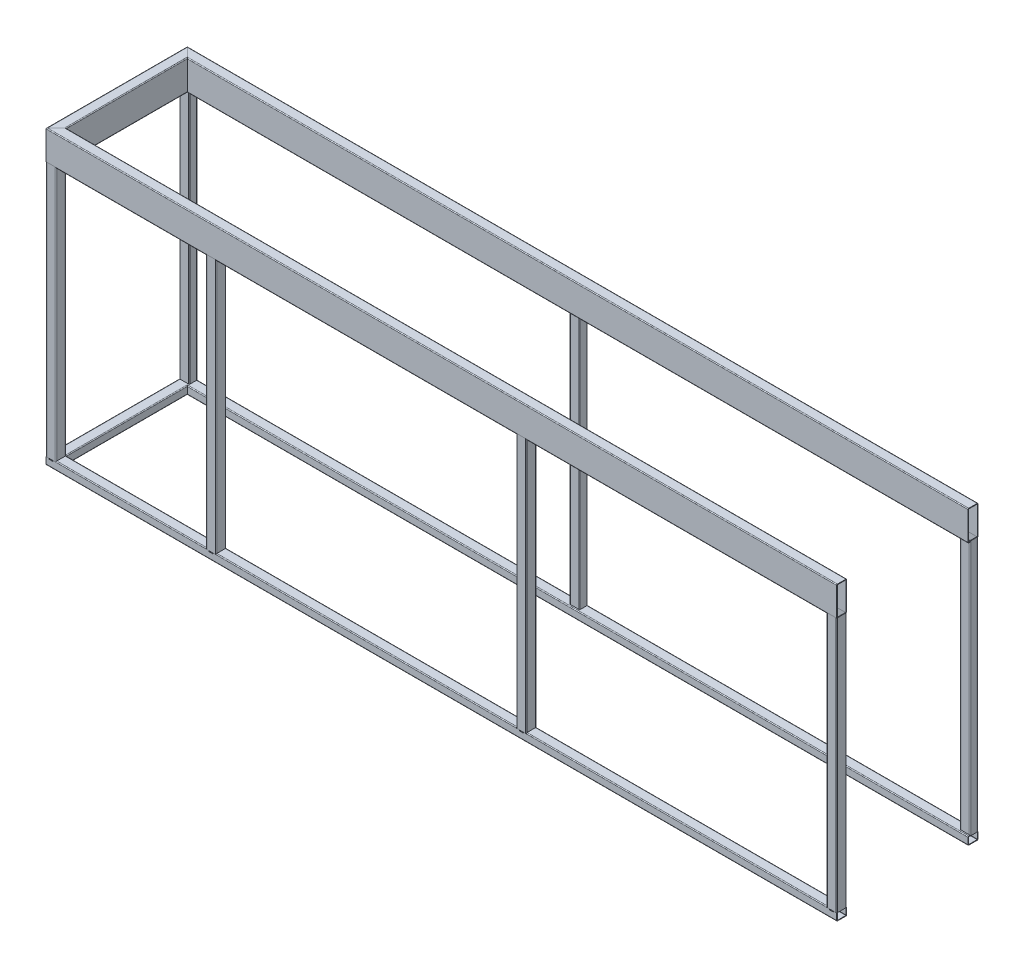
SolidWorks part; units mm, degrees
material "1.4301 (X5CrNi18-10)"
ref_plane "Ebene vorne" through (0, 0, 0) normal (0, 0, 1) x (1, 0, 0)
ref_plane "Ebene oben" through (0, 0, 0) normal (0, 1, 0) x (1, 0, 0)
ref_plane "Ebene rechts" through (0, 0, 0) normal (1, 0, 0) x (0, 0, -1)
sketch3d "3D-Skizze1"
  line L0 (0, 0, 0) -> (3901, 0, 0)
  line L1 (0, 0, 0) -> (0, 0, -656)
  line L2 (0, 0, -656) -> (3901, 0, -656)
  line L3 (0, 0, 0) -> (0, -1363, 0)
  line L4 (0, -1363, 0) -> (3901, -1363, 0)
  line L5 (3901, -1363, 0) -> (3901, 0, 0)
  line L6 (800, -1363, 0) -> (800, 0, 0)
  line L7 (2350, -1363, 0) -> (2350, 0, 0)
  line L9 (0, -1363, -656) -> (3901, -1363, -656)
  line L11 (0, -1363, -656) -> (0, -1363, 0)
  line L12 (0, -1363, -656) -> (0, -1363, -661) construction
  line L13 (0, 0, -656) -> (0, 0, -661) construction
  line L14 (0, 0, -661) -> (0, -1363, -661)
  line L15 (3901, 0, -656) -> (3901, 0, -661) construction
  line L16 (3901, -1363, -656) -> (3901, -1363, -661) construction
  line L17 (1950.5, -1363, -656) -> (1950.5, -1363, -661) construction
  line L18 (1950.5, 0, -656) -> (1950.5, 0, -661) construction
  line L19 (3901, 0, -661) -> (3901, -1363, -661)
  line L20 (1950.5, -1363, -661) -> (1950.5, 0, -661)
  dimension "D1" = 1551
  dimension "D6" = 5
  dimension "D2" = 656
  dimension "D3" = 1363
  dimension "D4" = 800
  dimension "D5" = 1550
other "Vierkantrohre 150X50X3(1)"
ref_plane "Ebene1" through (0, 0, -656) normal (1, 0, 0) x (0, 1, 0)
sketch "Skizze1" plane through (0, 0, -656) normal (1, 0, 0) x (0, 1, 0)
  line L1 (-71, 22) -> (71, 22)
  line L2 (-72, 21) -> (-72, -21)
  line L3 (-71, -22) -> (71, -22)
  line L4 (72, 21) -> (72, -21)
  line L5 (-72, 22) -> (72, -22) construction
  line L6 (-72, -22) -> (72, 22) construction
  line L7 (-71, 25) -> (71, 25)
  line L8 (-75, 21) -> (-75, -21)
  line L9 (-71, -25) -> (71, -25)
  line L10 (75, 21) -> (75, -21)
  line L11 (-75, 25) -> (75, -25) construction
  line L12 (-75, -25) -> (75, 25) construction
  arc A0 (71, -22) -> (72, -21) centre (71, -21) ccw
  arc A1 (71, -25) -> (75, -21) centre (71, -21) ccw
  arc A2 (-72, -21) -> (-71, -22) centre (-71, -21) ccw
  arc A3 (-75, -21) -> (-71, -25) centre (-71, -21) ccw
  arc A4 (-71, 22) -> (-72, 21) centre (-71, 21) ccw
  arc A5 (-71, 25) -> (-75, 21) centre (-71, 21) ccw
  arc A6 (71, 22) -> (72, 21) centre (71, 21) cw
  arc A7 (71, 25) -> (75, 21) centre (71, 21) cw
  point P0 (0, 0)
  point P6 (0, 0)
  point P35 (0, 0)
  dimension "D5" = 1
  dimension "D6" = 4
  dimension "D1" = 150
  dimension "D2" = 50
  dimension "D3" = 3
  dimension "D4" = 3
other "Vierkantrohre 50X50X3(1)"
ref_plane "Ebene2" through (0, 0, 0) normal (0, -1, 0) x (1, 0, 0)
sketch "Skizze13" plane through (0, 0, 0) normal (0, -1, 0) x (1, 0, 0)
  line L1 (-21, 22) -> (21, 22)
  line L2 (-22, 21) -> (-22, -21)
  line L3 (-21, -22) -> (21, -22)
  line L4 (22, 21) -> (22, -21)
  line L5 (-22, 22) -> (22, -22) construction
  line L6 (-22, -22) -> (22, 22) construction
  line L7 (-21, 25) -> (21, 25)
  line L8 (-25, 21) -> (-25, -21)
  line L9 (-21, -25) -> (21, -25)
  line L10 (25, 21) -> (25, -21)
  line L11 (-25, 25) -> (25, -25) construction
  line L12 (-25, -25) -> (25, 25) construction
  arc A0 (21, -22) -> (22, -21) centre (21, -21) ccw
  arc A1 (21, -25) -> (25, -21) centre (21, -21) ccw
  arc A2 (-22, -21) -> (-21, -22) centre (-21, -21) ccw
  arc A3 (-25, -21) -> (-21, -25) centre (-21, -21) ccw
  arc A4 (-21, 22) -> (-22, 21) centre (-21, 21) ccw
  arc A5 (-21, 25) -> (-25, 21) centre (-21, 21) ccw
  arc A6 (21, 22) -> (22, 21) centre (21, 21) cw
  arc A7 (21, 25) -> (25, 21) centre (21, 21) cw
  point P0 (0, 0)
  point P6 (0, 0)
  point P35 (0, 0)
  dimension "D5" = 1
  dimension "D6" = 4
  dimension "D1" = 50
  dimension "D2" = 50
  dimension "D3" = 3
  dimension "D4" = 3
other "Vierkantrohre 40X50X3(1)"
ref_plane "Ebene3" through (0, -1363, -656) normal (1, 0, 0) x (0, 1, 0)
sketch "Skizze15" plane through (0, -1363, -656) normal (1, 0, 0) x (0, 1, 0)
  line L1 (-16, 22) -> (16, 22)
  line L2 (-17, 21) -> (-17, -21)
  line L3 (-16, -22) -> (16, -22)
  line L4 (17, 21) -> (17, -21)
  line L5 (-17, 22) -> (17, -22) construction
  line L6 (-17, -22) -> (17, 22) construction
  line L7 (-16, 25) -> (16, 25)
  line L8 (-20, 21) -> (-20, -21)
  line L9 (-16, -25) -> (16, -25)
  line L10 (20, 21) -> (20, -21)
  line L11 (-20, 25) -> (20, -25) construction
  line L12 (-20, -25) -> (20, 25) construction
  arc A0 (16, -22) -> (17, -21) centre (16, -21) ccw
  arc A1 (16, -25) -> (20, -21) centre (16, -21) ccw
  arc A2 (-17, -21) -> (-16, -22) centre (-16, -21) ccw
  arc A3 (-20, -21) -> (-16, -25) centre (-16, -21) ccw
  arc A4 (-16, 22) -> (-17, 21) centre (-16, 21) ccw
  arc A5 (-16, 25) -> (-20, 21) centre (-16, 21) ccw
  arc A6 (16, 22) -> (17, 21) centre (16, 21) cw
  arc A7 (16, 25) -> (20, 21) centre (16, 21) cw
  point P0 (0, 0)
  point P6 (0, 0)
  point P35 (0, 0)
  dimension "D5" = 1
  dimension "D6" = 4
  dimension "D1" = 40
  dimension "D2" = 50
  dimension "D3" = 3
  dimension "D4" = 3
other "Trimmen/Verlängern2"
sketch "Skizze16" plane through (0, 0, 25) normal (0, 0, 1) x (1, 0, 0)
  line L0 (25, -1343) -> (25, -1347)
  line L1 (-21, -1343) -> (3926, -1343) construction
  line L2 (25, -1363) -> (25, 0) construction
  line L3 (-25, -1347) -> (3926, -1347) construction
  line L4 (25, -1347) -> (10, -1347)
  line L5 (-25, -1347) -> (-25, -1343)
  line L6 (-25, -1343) -> (25, -1343)
  line L7 (775, -1343) -> (775, -1347)
  line L8 (775, -1347) -> (790, -1347)
  line L9 (825, -1363) -> (825, 0) construction
  line L10 (825, -1347) -> (825, -1343)
  line L11 (825, -1343) -> (775, -1343)
  line L12 (775, -1363) -> (775, 0) construction
  line L14 (25, -71) -> (25, -75)
  line L18 (25, -75) -> (-25, -75)
  line L19 (2325, -1347) -> (2340, -1347)
  line L20 (2375, -1347) -> (2375, -1343)
  line L21 (2375, -1343) -> (2325, -1343)
  line L22 (2325, -1343) -> (2325, -1347)
  line L23 (2325, -1363) -> (2325, 0) construction
  line L24 (-25, -75) -> (-25, -71)
  line L25 (2375, -1363) -> (2375, 0) construction
  line L26 (3876, -1343) -> (3876, -1347)
  line L27 (3876, -1363) -> (3876, 0) construction
  line L28 (3876, -1347) -> (3891, -1347)
  line L29 (3926, -1347) -> (3926, -1343)
  line L30 (3926, -1343) -> (3876, -1343)
  line L31 (-25, -71) -> (25, -71)
  line L32 (775, -71) -> (775, -75)
  line L33 (775, -75) -> (825, -75)
  line L34 (825, -75) -> (825, -71)
  line L35 (825, -71) -> (775, -71)
  line L36 (2325, -75) -> (2375, -75)
  line L37 (2375, -75) -> (2375, -71)
  line L38 (2375, -71) -> (2325, -71)
  line L39 (2325, -71) -> (2325, -75)
  line L40 (3876, -71) -> (3876, -75)
  line L41 (3876, -75) -> (3926, -75)
  line L42 (3926, -75) -> (3926, -71)
  line L43 (3926, -71) -> (3876, -71)
  line L44 (-21, -75) -> (3926, -75) construction
  line L45 (-10, -1347) -> (-10, -1351)
  line L46 (-10, -1351) -> (10, -1351)
  line L47 (10, -1351) -> (10, -1347)
  line L48 (790, -1347) -> (790, -1351)
  line L49 (790, -1351) -> (810, -1351)
  line L50 (810, -1351) -> (810, -1347)
  line L51 (2340, -1347) -> (2340, -1351)
  line L52 (2340, -1351) -> (2360, -1351)
  line L53 (2360, -1351) -> (2360, -1347)
  line L54 (3891, -1347) -> (3891, -1351)
  line L55 (3891, -1351) -> (3911, -1351)
  line L56 (3911, -1351) -> (3911, -1347)
  line L57 (3911, -1347) -> (3926, -1347)
  line L58 (2360, -1347) -> (2375, -1347)
  line L59 (810, -1347) -> (825, -1347)
  line L60 (-10, -1347) -> (-25, -1347)
  dimension "D2" = 20
  dimension "D3" = 4
  dimension "D4" = 15
  dimension "D5" = 15
  dimension "D6" = 20
  dimension "D7" = 4
  dimension "D8" = 4
  dimension "D9" = 15
  dimension "D10" = 20
  dimension "D11" = 20
  dimension "D12" = 4
  dimension "D13" = 15
  dimension "D1" = 2
extrude "Schnitt-Linear austragen1" cut sketch "Skizze16" against normal blind 50
sketch "Skizze17" plane through (0, 0, -681) normal (0, 0, -1) x (-1, 0, 0)
  line L0 (-3876, -1343) -> (-3876, -1347)
  line L1 (-3926, -1347) -> (25, -1347) construction
  line L2 (-3876, -1347) -> (-3926, -1347)
  line L3 (-3926, -1347) -> (-3926, -1343)
  line L4 (-3926, -1343) -> (-3876, -1343)
  line L5 (-1975.5, -1343) -> (-1925.5, -1343)
  line L6 (-3926, -1343) -> (21, -1343) construction
  line L8 (-1925.5, -1343) -> (-1925.5, -1347)
  line L9 (-1925.5, -1347) -> (-1975.5, -1347)
  line L10 (-1975.5, -1347) -> (-1975.5, -1343)
  line L12 (-25, -1343) -> (25, -1343)
  line L14 (25, -1343) -> (25, -1347)
  line L15 (25, -1347) -> (-25, -1347)
  line L16 (-25, -1347) -> (-25, -1343)
  line L17 (-3876, -71) -> (-3876, -75)
  line L18 (25, -1363) -> (25, 0) construction
  line L21 (-3876, -75) -> (-3926, -75)
  line L22 (-3926, -75) -> (-3926, -71)
  line L23 (-3926, -71) -> (-3876, -71)
  line L24 (-1975.5, -71) -> (-1925.5, -71)
  line L25 (-1925.5, -71) -> (-1925.5, -75)
  line L26 (-1925.5, -75) -> (-1975.5, -75)
  line L27 (-1975.5, -75) -> (-1975.5, -71)
  line L28 (-25, -71) -> (25, -71)
  line L29 (25, -71) -> (25, -75)
  line L30 (25, -75) -> (-25, -75)
  line L31 (-25, -75) -> (-25, -71)
  line L32 (-3926, -75) -> (21, -75) construction
  dimension "D2" = 1900.5
  dimension "D3" = 50
  dimension "D4" = 50
  dimension "D5" = 50
  dimension "D6" = 4
  dimension "D1" = 2
extrude "Schnitt-Linear austragen2" cut sketch "Skizze17" against normal blind 40
other "Trimmen/Verlängern5"
other "Vierkantrohre 40X50X3(5)"
ref_plane "Ebene4" through (3901, 0, -661) normal (0, -1, 0) x (0, 0, 1)
sketch "Skizze19" plane through (3901, 0, -661) normal (0, -1, 0) x (0, 0, 1)
  line L1 (-16, 22) -> (16, 22)
  line L2 (-17, 21) -> (-17, -21)
  line L3 (-16, -22) -> (16, -22)
  line L4 (17, 21) -> (17, -21)
  line L5 (-17, 22) -> (17, -22) construction
  line L6 (-17, -22) -> (17, 22) construction
  line L7 (-16, 25) -> (16, 25)
  line L8 (-20, 21) -> (-20, -21)
  line L9 (-16, -25) -> (16, -25)
  line L10 (20, 21) -> (20, -21)
  line L11 (-20, 25) -> (20, -25) construction
  line L12 (-20, -25) -> (20, 25) construction
  arc A0 (16, -22) -> (17, -21) centre (16, -21) ccw
  arc A1 (16, -25) -> (20, -21) centre (16, -21) ccw
  arc A2 (-17, -21) -> (-16, -22) centre (-16, -21) ccw
  arc A3 (-20, -21) -> (-16, -25) centre (-16, -21) ccw
  arc A4 (-16, 22) -> (-17, 21) centre (-16, 21) ccw
  arc A5 (-16, 25) -> (-20, 21) centre (-16, 21) ccw
  arc A6 (16, 22) -> (17, 21) centre (16, 21) cw
  arc A7 (16, 25) -> (20, 21) centre (16, 21) cw
  point P0 (0, 0)
  point P6 (0, 0)
  point P35 (0, 0)
  dimension "D5" = 1
  dimension "D6" = 4
  dimension "D1" = 40
  dimension "D2" = 50
  dimension "D3" = 3
  dimension "D4" = 3
other "Trimmen/Verlängern6"
